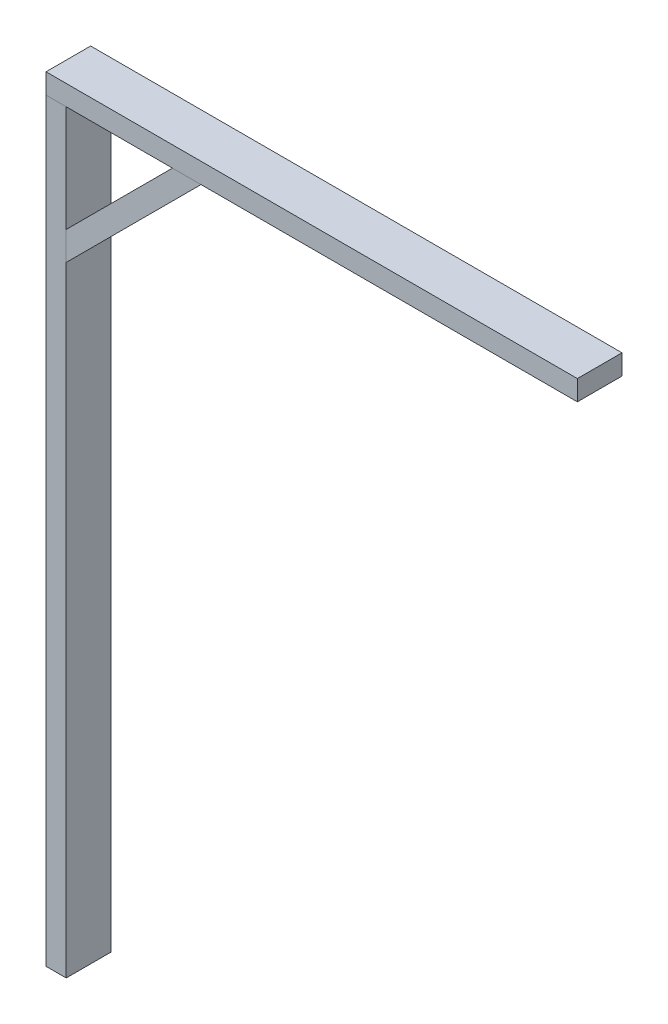
SolidWorks part; units mm, degrees
ref_plane "Alzado" through (0, 0, 0) normal (0, 0, 1) x (1, 0, 0)
ref_plane "Planta" through (0, 0, 0) normal (0, 1, 0) x (1, 0, 0)
ref_plane "Vista lateral" through (0, 0, 0) normal (1, 0, 0) x (0, 0, -1)
sketch "Croquis1" plane through (0, 0, 0) normal (0, 1, 0) x (1, 0, 0)
  line L1 (9.5, -21) -> (-9.5, -21)
  line L2 (9.5, -21) -> (9.5, 21)
  line L3 (9.5, 21) -> (-9.5, 21)
  line L4 (-9.5, -21) -> (-9.5, 21)
  line L5 (9.5, -21) -> (-9.5, 21) construction
  line L6 (9.5, 21) -> (-9.5, -21) construction
  point P0 (0, 0)
  dimension "D1" = 19
  dimension "D2" = 42
extrude "Saliente-Extruir1" add sketch "Croquis1" along normal blind 710
sketch "Croquis2" plane through (-9.5, 0, 0) normal (-1, 0, 0) x (0, 0, 1)
  line L0 (21, 710) -> (21, 0) construction
  line L1 (-21, 710) -> (21, 710)
  line L2 (-21, 710) -> (-21, 729)
  line L3 (-21, 729) -> (21, 729)
  line L4 (21, 710) -> (21, 729)
  dimension "D1" = 19
extrude "Saliente-Extruir2" add sketch "Croquis2" against normal blind 500 separate body
sketch "Croquis3" plane through (0, 0, 21) normal (0, 0, 1) x (1, 0, 0)
  line L0 (9.5, 610) -> (9.5, 583.1299)
  line L1 (9.5, 710) -> (9.5, 0) construction
  line L2 (109.5, 710) -> (136.3701, 710)
  line L3 (490.5, 710) -> (-9.5, 710) construction
  line L4 (109.5, 710) -> (9.5, 610)
  line L5 (136.3701, 710) -> (9.5, 583.1299)
  dimension "D1" = 19
  dimension "D3" = 100
  dimension "D4" = 100
extrude "Saliente-Extruir3" add sketch "Croquis3" against normal up to surface (42 mm away) separate body up to face at (240.5, 719.5, -21)
